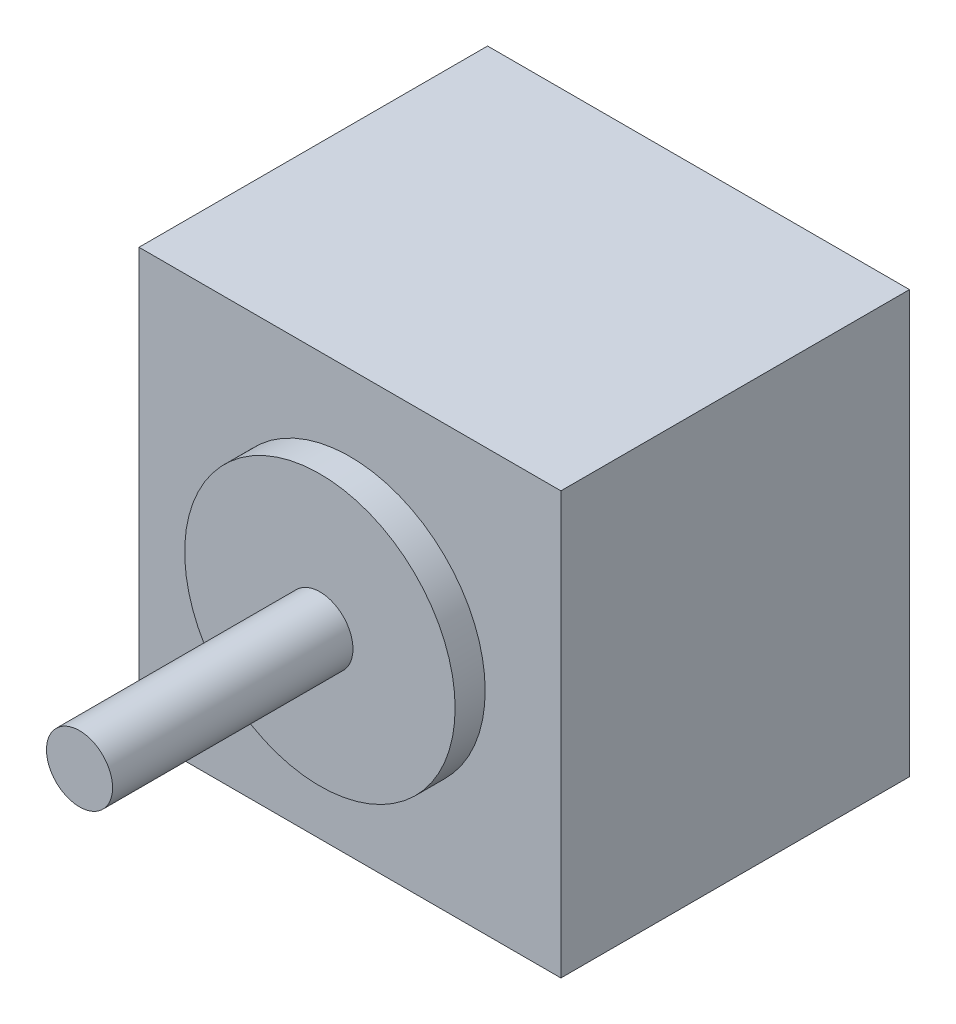
SolidWorks part; units mm, degrees
ref_plane "Front Plane" through (0, 0, 0) normal (0, 0, 1) x (1, 0, 0)
ref_plane "Top Plane" through (0, 0, 0) normal (0, 1, 0) x (1, 0, 0)
ref_plane "Right Plane" through (0, 0, 0) normal (1, 0, 0) x (0, 0, -1)
sketch "Sketch1" plane through (0, 0, 0) normal (0, 0, 1) x (1, 0, 0)
  line L1 (-13.1625, 8.55) -> (21.9375, 8.55)
  line L2 (-13.1625, 8.55) -> (-13.1625, -26.55)
  line L3 (-13.1625, -26.55) -> (21.9375, -26.55)
  line L4 (21.9375, 8.55) -> (21.9375, -26.55)
  dimension "D1" = 35.1
  dimension "D2" = 35.1
extrude "Boss-Extrude1" add sketch "Sketch1" along normal blind 29 contours L1 L4 L3 L2
sketch "Sketch2" plane through (0, 0, 29) normal (0, 0, 1) x (1, 0, 0)
  circle A0 centre (4.3875, -9) radius 11.25
extrude "Boss-Extrude2" add sketch "Sketch2" along normal blind 2.5
sketch "Sketch3" plane through (0, 0, 31.5) normal (0, 0, 1) x (1, 0, 0)
  circle A0 centre (4.3875, -9) radius 2.75
extrude "Boss-Extrude3" add sketch "Sketch3" along normal blind 20
